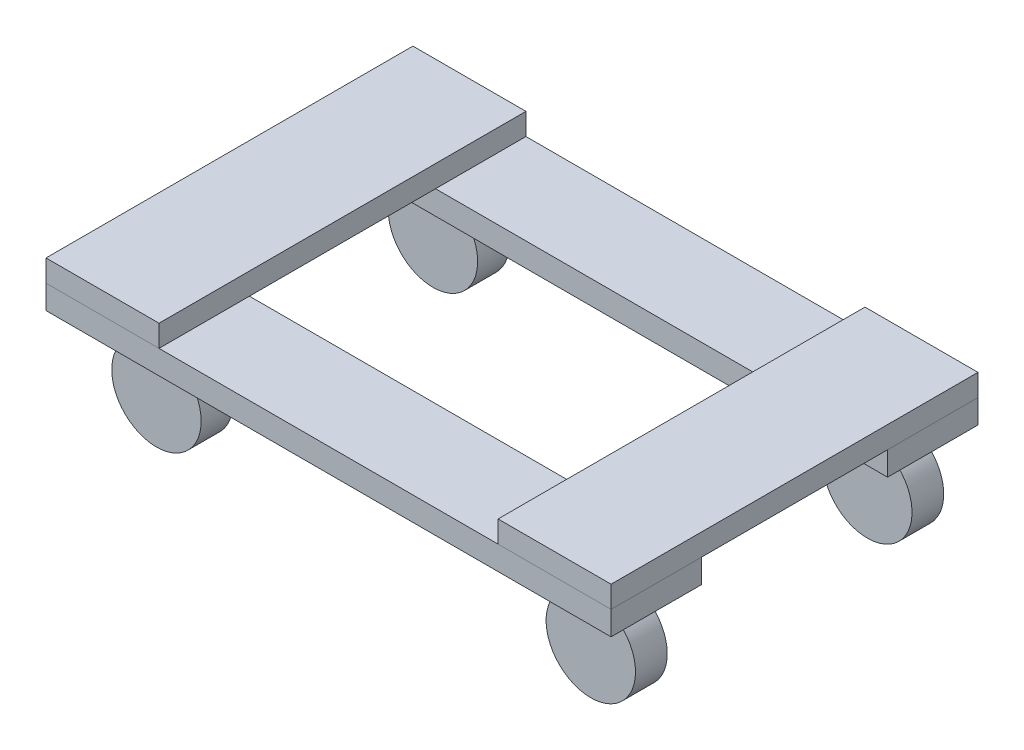
SolidWorks part; units mm, degrees
ref_plane "Front" through (0, 0, 0) normal (0, 0, 1) x (1, 0, 0)
ref_plane "Top" through (0, 0, 0) normal (0, 1, 0) x (1, 0, 0)
ref_plane "Right" through (0, 0, 0) normal (1, 0, 0) x (0, 0, -1)
sketch "Sketch1" plane through (0, 0, 0) normal (0, 1, 0) x (1, 0, 0)
  line L0 (226.2188, 72.39) -> (221.9376, -221.2663) construction
  line L1 (0, 0) -> (452.4375, 0)
  line L2 (0, 0) -> (0, 72.39)
  line L3 (0, 72.39) -> (452.4375, 72.39)
  line L4 (452.4375, 0) -> (452.4375, 72.39)
  line L5 (0, 0) -> (452.4375, 72.39) construction
  line L6 (0, 72.39) -> (452.4375, 0) construction
  line L8 (0, -221.392) -> (452.4375, -221.392)
  line L9 (0, -221.392) -> (0, -149.002)
  line L10 (0, -149.002) -> (452.4375, -149.002)
  line L11 (452.4375, -221.392) -> (452.4375, -149.002)
  line L12 (0, -221.392) -> (452.4375, -149.002) construction
  line L13 (0, -149.002) -> (452.4375, -221.392) construction
  point P4 (226.2188, 36.195)
  point P12 (226.2187, -185.197)
  dimension "D1" = 452.4375
  dimension "D2" = 72.39
  dimension "D3" = 293.6875
extrude "Boss-Extrude1" add sketch "Sketch1" along normal blind 19.05
sketch "Sketch2" plane through (0, 19.05, 0) normal (0, 1, 0) x (1, 0, 0)
  line L0 (452.4375, 72.39) -> (0, 72.39) construction
  line L1 (452.4375, -221.392) -> (361.95, -221.392)
  line L2 (452.4375, -221.392) -> (452.4375, 72.39)
  line L3 (452.4375, 72.39) -> (361.95, 72.39)
  line L4 (361.95, -221.392) -> (361.95, 72.39)
  line L5 (452.4375, -221.392) -> (361.95, 72.39) construction
  line L6 (452.4375, 72.39) -> (361.95, -221.392) construction
  line L8 (0, -221.392) -> (90.4875, -221.392)
  line L9 (0, -221.392) -> (0, 72.39)
  line L10 (0, 72.39) -> (90.4875, 72.39)
  line L11 (90.4875, -221.392) -> (90.4875, 72.39)
  line L12 (0, -221.392) -> (90.4875, 72.39) construction
  line L13 (0, 72.39) -> (90.4875, -221.392) construction
  point P4 (407.1938, -74.501)
  point P12 (45.2437, -74.501)
  dimension "D1" = 90.4875
extrude "Boss-Extrude2" add sketch "Sketch2" along normal blind 17.4625 separate body
ref_plane "Plane1" through (0, 0, 185.197) normal (0, 0, 1) x (1, 0, 0)
sketch "Sketch3" plane through (0, 0, 185.197) normal (0, 0, 1) x (1, 0, 0)
  circle A0 centre (64.9416, -38.0904) radius 35.7892
  circle A1 centre (412.7094, -38.0904) radius 35.7892
extrude "Boss-Extrude3" add sketch "Sketch3" along normal blind 12.7 and the other way blind 12.7 separate body
ref_plane "Plane3" through (0, 0, -36.195) normal (0, 0, -1) x (-1, 0, 0)
sketch "Sketch4" plane through (0, 0, -36.195) normal (0, 0, -1) x (-1, 0, 0)
  circle A1 centre (-64.9416, -38.0904) radius 35.7892
  circle A2 centre (-64.9416, -38.0904) radius 35.7892
  circle A3 centre (-412.7094, -38.0904) radius 35.7892
  circle A4 centre (-412.7094, -38.0904) radius 35.7892
  dimension "D1" = 0
  dimension "D2" = 0
extrude "Boss-Extrude4" add sketch "Sketch4" along normal blind 12.7 and the other way blind 12.7 separate body
